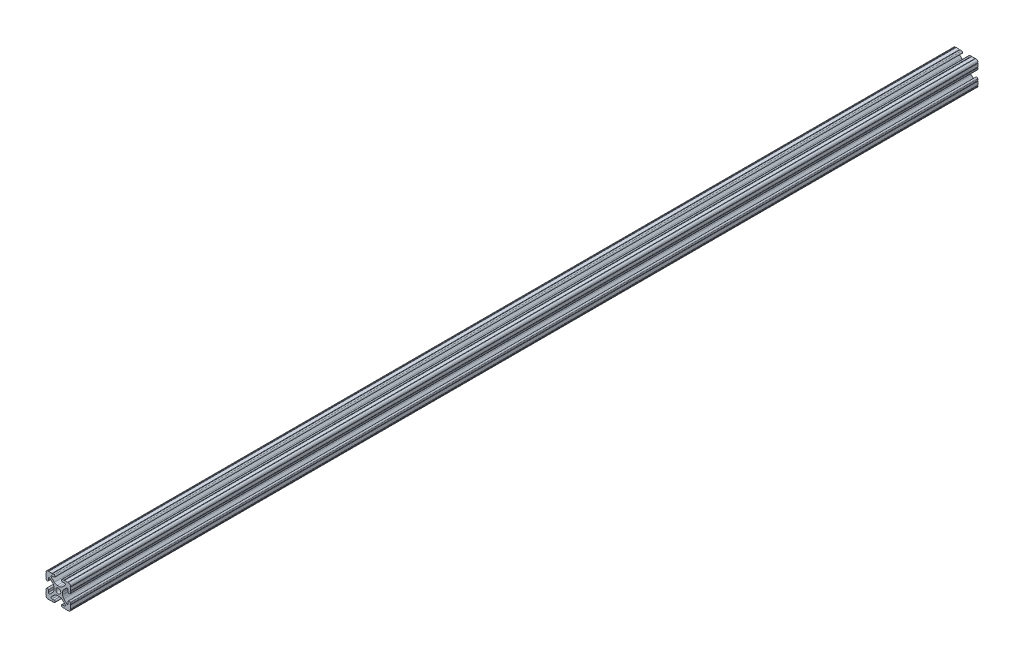
SolidWorks part; units mm, degrees
ref_plane "Front Plane" through (0, 0, 0) normal (0, 0, 1) x (1, 0, 0)
ref_plane "Top Plane" through (0, 0, 0) normal (0, 1, 0) x (1, 0, 0)
ref_plane "Right Plane" through (0, 0, 0) normal (1, 0, 0) x (0, 0, -1)
sketch "Sketch1" plane through (0, 0, 0) normal (0, 0, 1) x (1, 0, 0)
  line L0 (0, 12.7) -> (-12.7814, 12.7) construction
  line L1 (-4.5085, 0) -> (-4.5085, 2.9459)
  line L2 (-6.0437, 12.5461) -> (-10.0976, 12.6876) construction
  line L3 (-11.5616, 12.4229) -> (-4.3159, 12.1699) construction
  line L4 (-6.4364, 10.3486) -> (-6.3592, 12.5571) construction
  line L6 (-2.9459, 4.5085) -> (0, 4.5085)
  line L7 (0, 0) -> (0, 12.7) construction
  line L8 (0, 0) -> (-12.7814, 0) construction
  line L9 (0.7813, 0.7813) -> (-0.7813, -0.7813) construction
  line L10 (-2.9459, 4.5085) -> (-7.1484, 8.711)
  line L11 (-4.5085, 2.9459) -> (-8.711, 7.1484)
  line L13 (0, 0) -> (-12.7814, 12.7814) construction
  line L14 (-10.4131, 12.6987) -> (-4.3048, 12.4853)
  line L15 (-4.3048, 12.4853) -> (-4.382, 10.2769) construction
  line L16 (-4.382, 10.2769) -> (-6.4364, 10.3486)
  line L17 (-12.6987, 10.4131) -> (-12.4853, 4.3048)
  line L18 (-10.2769, 4.382) -> (-10.3486, 6.4364)
  circle A0 centre (0, 0) radius 2.6035
  arc A1 (-4.382, 10.2769) -> (-4.3048, 12.4853) centre (-4.3434, 11.3811) ccw
  arc A2 (-7.1484, 8.711) -> (-6.4364, 10.3486) centre (-6.4698, 9.3896) cw
  arc A3 (-8.711, 7.1484) -> (-10.3486, 6.4364) centre (-9.3896, 6.4698) ccw
  arc A4 (-10.2769, 4.382) -> (-12.4853, 4.3048) centre (-11.3811, 4.3434) cw
  arc A5 (-10.4131, 12.6987) -> (-12.6987, 10.4131) centre (-10.4902, 10.4902) ccw
  arc A6 (-10.4131, 12.6987) -> (-9.7821, 12.6766) centre (-10.0976, 12.6876) ccw
  arc A7 (-6.3592, 12.5571) -> (-5.7282, 12.5351) centre (-6.0437, 12.5461) ccw
  arc A8 (-12.5571, 6.3592) -> (-12.5351, 5.7282) centre (-12.5461, 6.0437) cw
  arc A9 (-12.6987, 10.4131) -> (-12.6766, 9.7821) centre (-12.6876, 10.0976) cw
  dimension "D1" = 5.207
  dimension "D5" = 14.859
  dimension "D9" = 2
  dimension "D2" = 25.4
  dimension "D12" = 0.6314
  dimension "D10" = 2.2098
  dimension "D3" = 9.017
  dimension "D4" = 9.017
  dimension "D6" = 25.4
  dimension "D7" = 6.477
  dimension "D8" = 2.2098
  dimension "D11" = 12.7
sketch "Sketch3" plane through (0, 0, 0) normal (0, 0, 1) x (1, 0, 0)
  line L0 (-2.9459, 4.5085) -> (0, 4.5085) construction
  line L1 (-2.9459, 4.5085) -> (-7.1484, 8.711) construction
  line L2 (-4.382, 10.2769) -> (-6.4364, 10.3486) construction
  line L3 (-10.4131, 12.6987) -> (-4.3048, 12.4853) construction
  line L4 (-4.5085, 0) -> (-4.5085, 2.9459) construction
  line L5 (-4.5085, 2.9459) -> (-8.711, 7.1484) construction
  line L6 (-10.2769, 4.382) -> (-10.3486, 6.4364) construction
  line L7 (-12.6987, 10.4131) -> (-12.4853, 4.3048) construction
  line L8 (-1.1153, 4.5085) -> (1.1153, 4.5085)
  line L9 (-4.2404, 5.803) -> (-7.1484, 8.711)
  line L10 (-4.382, 10.2769) -> (-6.4364, 10.3486)
  line L11 (-9.7821, 12.6766) -> (-6.3592, 12.5571)
  line L12 (-4.5085, -1.1153) -> (-4.5085, 1.1153)
  line L13 (-5.803, 4.2404) -> (-8.711, 7.1484)
  line L14 (-10.2769, 4.382) -> (-10.3486, 6.4364)
  line L15 (-12.6766, 9.7821) -> (-12.5571, 6.3592)
  line L16 (-5.7282, 12.5351) -> (-4.3048, 12.4853)
  line L17 (-12.5351, 5.7282) -> (-12.4853, 4.3048)
  line L18 (0, 0) -> (0, 12.7) construction
  line L19 (0, 0) -> (-12.7814, 0) construction
  line L20 (12.5351, 5.7282) -> (12.4853, 4.3048)
  line L21 (5.7282, 12.5351) -> (4.3048, 12.4853)
  line L22 (12.6766, 9.7821) -> (12.5571, 6.3592)
  line L23 (10.2769, 4.382) -> (10.3486, 6.4364)
  line L24 (5.803, 4.2404) -> (8.711, 7.1484)
  line L25 (4.5085, -1.1153) -> (4.5085, 1.1153)
  line L26 (9.7821, 12.6766) -> (6.3592, 12.5571)
  line L27 (4.382, 10.2769) -> (6.4364, 10.3486)
  line L28 (4.2404, 5.803) -> (7.1484, 8.711)
  line L29 (4.2404, -5.803) -> (7.1484, -8.711)
  line L30 (4.382, -10.2769) -> (6.4364, -10.3486)
  line L31 (9.7821, -12.6766) -> (6.3592, -12.5571)
  line L32 (5.803, -4.2404) -> (8.711, -7.1484)
  line L33 (10.2769, -4.382) -> (10.3486, -6.4364)
  line L34 (12.6766, -9.7821) -> (12.5571, -6.3592)
  line L35 (5.7282, -12.5351) -> (4.3048, -12.4853)
  line L36 (12.5351, -5.7282) -> (12.4853, -4.3048)
  line L37 (-12.5351, -5.7282) -> (-12.4853, -4.3048)
  line L38 (-5.7282, -12.5351) -> (-4.3048, -12.4853)
  line L39 (-12.6766, -9.7821) -> (-12.5571, -6.3592)
  line L40 (-10.2769, -4.382) -> (-10.3486, -6.4364)
  line L41 (-5.803, -4.2404) -> (-8.711, -7.1484)
  line L42 (-9.7821, -12.6766) -> (-6.3592, -12.5571)
  line L43 (-4.382, -10.2769) -> (-6.4364, -10.3486)
  line L44 (-4.2404, -5.803) -> (-7.1484, -8.711)
  line L45 (-1.1153, -4.5085) -> (1.1153, -4.5085)
  arc A0 (-10.4131, 12.6987) -> (-9.7821, 12.6766) centre (-10.0976, 12.6876) ccw construction
  arc A1 (-6.4364, 10.3486) -> (-7.1484, 8.711) centre (-6.4698, 9.3896) ccw construction
  arc A2 (-4.382, 10.2769) -> (-4.3048, 12.4853) centre (-4.3434, 11.3811) ccw construction
  arc A3 (-8.711, 7.1484) -> (-10.3486, 6.4364) centre (-9.3896, 6.4698) ccw construction
  arc A4 (-12.4853, 4.3048) -> (-10.2769, 4.382) centre (-11.3811, 4.3434) ccw construction
  arc A5 (-6.3592, 12.5571) -> (-5.7282, 12.5351) centre (-6.0437, 12.5461) ccw construction
  arc A6 (-10.4131, 12.6987) -> (-12.6987, 10.4131) centre (-10.4902, 10.4902) ccw construction
  arc A7 (-12.6766, 9.7821) -> (-12.6987, 10.4131) centre (-12.6876, 10.0976) ccw construction
  arc A8 (-12.5351, 5.7282) -> (-12.5571, 6.3592) centre (-12.5461, 6.0437) ccw construction
  arc A9 (-10.4131, 12.6987) -> (-9.7821, 12.6766) centre (-10.0976, 12.6876) ccw
  arc A10 (-6.4364, 10.3486) -> (-7.1484, 8.711) centre (-6.4698, 9.3896) ccw
  arc A11 (-4.382, 10.2769) -> (-4.3048, 12.4853) centre (-4.3434, 11.3811) ccw
  arc A12 (-8.711, 7.1484) -> (-10.3486, 6.4364) centre (-9.3896, 6.4698) ccw
  arc A13 (-12.4853, 4.3048) -> (-10.2769, 4.382) centre (-11.3811, 4.3434) ccw
  arc A14 (-6.3592, 12.5571) -> (-5.7282, 12.5351) centre (-6.0437, 12.5461) ccw
  arc A15 (-10.4131, 12.6987) -> (-12.6987, 10.4131) centre (-10.4902, 10.4902) ccw
  arc A16 (-12.6766, 9.7821) -> (-12.6987, 10.4131) centre (-12.6876, 10.0976) ccw
  arc A17 (-12.5351, 5.7282) -> (-12.5571, 6.3592) centre (-12.5461, 6.0437) ccw
  arc A18 (-1.1153, 4.5085) -> (-4.2404, 5.803) centre (-1.1153, 8.9281) cw
  arc A19 (4.5085, 1.1153) -> (5.803, 4.2404) centre (8.9281, 1.1153) cw
  arc A20 (1.1153, 4.5085) -> (4.2404, 5.803) centre (1.1153, 8.9281) ccw
  arc A21 (-4.5085, 1.1153) -> (-5.803, 4.2404) centre (-8.9281, 1.1153) ccw
  arc A22 (12.5351, 5.7282) -> (12.5571, 6.3592) centre (12.5461, 6.0437) cw
  arc A23 (12.6766, 9.7821) -> (12.6987, 10.4131) centre (12.6876, 10.0976) cw
  arc A24 (10.4131, 12.6987) -> (12.6987, 10.4131) centre (10.4902, 10.4902) cw
  arc A25 (6.3592, 12.5571) -> (5.7282, 12.5351) centre (6.0437, 12.5461) cw
  arc A26 (12.4853, 4.3048) -> (10.2769, 4.382) centre (11.3811, 4.3434) cw
  arc A27 (8.711, 7.1484) -> (10.3486, 6.4364) centre (9.3896, 6.4698) cw
  arc A28 (4.382, 10.2769) -> (4.3048, 12.4853) centre (4.3434, 11.3811) cw
  arc A29 (6.4364, 10.3486) -> (7.1484, 8.711) centre (6.4698, 9.3896) cw
  arc A30 (10.4131, 12.6987) -> (9.7821, 12.6766) centre (10.0976, 12.6876) cw
  arc A31 (10.4131, -12.6987) -> (9.7821, -12.6766) centre (10.0976, -12.6876) ccw
  arc A32 (6.4364, -10.3486) -> (7.1484, -8.711) centre (6.4698, -9.3896) ccw
  arc A33 (4.382, -10.2769) -> (4.3048, -12.4853) centre (4.3434, -11.3811) ccw
  arc A34 (8.711, -7.1484) -> (10.3486, -6.4364) centre (9.3896, -6.4698) ccw
  arc A35 (12.4853, -4.3048) -> (10.2769, -4.382) centre (11.3811, -4.3434) ccw
  arc A36 (6.3592, -12.5571) -> (5.7282, -12.5351) centre (6.0437, -12.5461) ccw
  arc A37 (10.4131, -12.6987) -> (12.6987, -10.4131) centre (10.4902, -10.4902) ccw
  arc A38 (12.6766, -9.7821) -> (12.6987, -10.4131) centre (12.6876, -10.0976) ccw
  arc A39 (12.5351, -5.7282) -> (12.5571, -6.3592) centre (12.5461, -6.0437) ccw
  arc A40 (-4.5085, -1.1153) -> (-5.803, -4.2404) centre (-8.9281, -1.1153) cw
  arc A41 (1.1153, -4.5085) -> (4.2404, -5.803) centre (1.1153, -8.9281) cw
  arc A42 (4.5085, -1.1153) -> (5.803, -4.2404) centre (8.9281, -1.1153) ccw
  arc A43 (-1.1153, -4.5085) -> (-4.2404, -5.803) centre (-1.1153, -8.9281) ccw
  arc A44 (-12.5351, -5.7282) -> (-12.5571, -6.3592) centre (-12.5461, -6.0437) cw
  arc A45 (-12.6766, -9.7821) -> (-12.6987, -10.4131) centre (-12.6876, -10.0976) cw
  arc A46 (-10.4131, -12.6987) -> (-12.6987, -10.4131) centre (-10.4902, -10.4902) cw
  arc A47 (-6.3592, -12.5571) -> (-5.7282, -12.5351) centre (-6.0437, -12.5461) cw
  arc A48 (-12.4853, -4.3048) -> (-10.2769, -4.382) centre (-11.3811, -4.3434) cw
  arc A49 (-8.711, -7.1484) -> (-10.3486, -6.4364) centre (-9.3896, -6.4698) cw
  arc A50 (-4.382, -10.2769) -> (-4.3048, -12.4853) centre (-4.3434, -11.3811) cw
  arc A51 (-6.4364, -10.3486) -> (-7.1484, -8.711) centre (-6.4698, -9.3896) cw
  arc A52 (-10.4131, -12.6987) -> (-9.7821, -12.6766) centre (-10.0976, -12.6876) cw
  circle A53 centre (0, 0) radius 2.6035 construction
  circle A54 centre (0, 0) radius 2.6035
  point P135 (4.5085, 0)
  dimension "D2" = 4.4196
extrude "Extrude1" add sketch "Sketch3" along normal mid plane 939.8
equation "\"D10@Sketch1\" = \"D8@Sketch1\""
equation "\"D11@Sketch1\" = \"D6@Sketch1\"/2"
equation "\"D12@Sketch1\" = \"D8@Sketch1\"/3.5"
equation "\"D2@Sketch3\" = \"D8@Sketch1\"*2"
